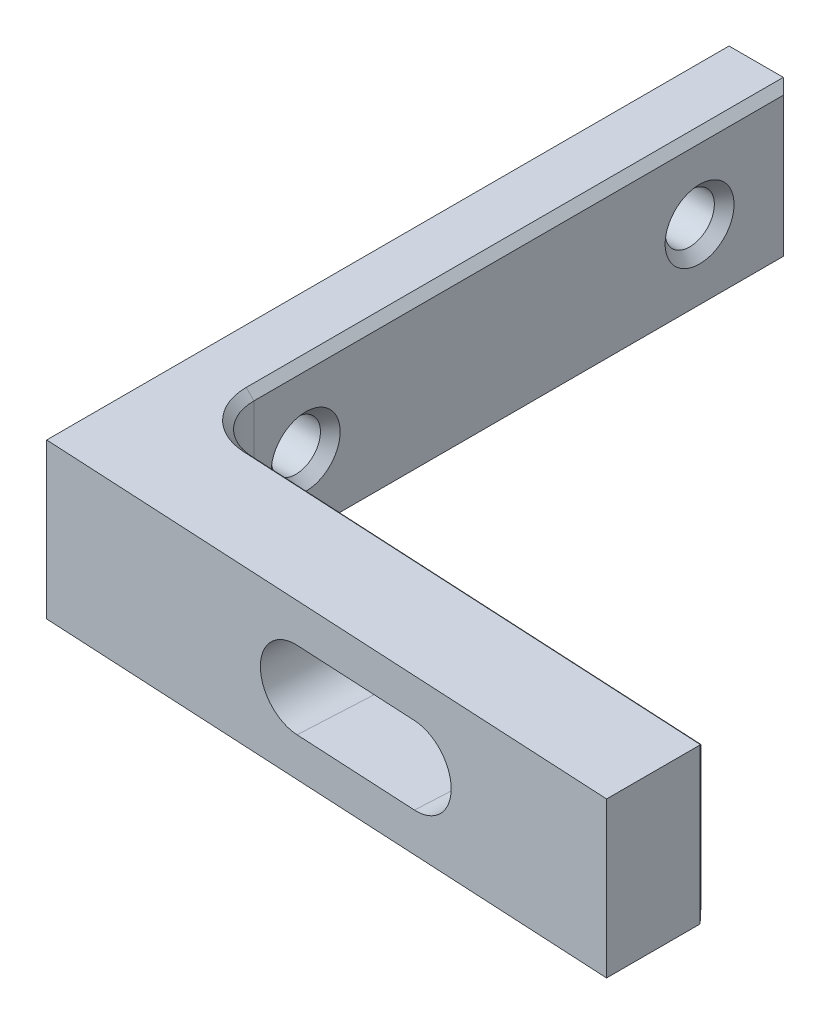
SolidWorks part; units mm, degrees
ref_plane "Front Plane" through (0, 0, 0) normal (0, 0, 1) x (1, 0, 0)
ref_plane "Top Plane" through (0, 0, 0) normal (0, 1, 0) x (1, 0, 0)
ref_plane "Right Plane" through (0, 0, 0) normal (1, 0, 0) x (0, 0, -1)
sketch "Sketch1" plane through (0, 0, 0) normal (0, 1, 0) x (1, 0, 0)
  line L1 (-19.05, -22) -> (19.05, -22)
  line L2 (-19.05, -22) -> (-19.05, 22)
  line L3 (-19.05, 22) -> (19.05, 22)
  line L4 (19.05, -22) -> (19.05, 22)
  line L5 (-19.05, -22) -> (19.05, 22) construction
  line L6 (-19.05, 22) -> (19.05, -22) construction
  point P0 (0, 0)
  dimension "D1" = 38.1
  dimension "D2" = 44
extrude "Boss-Extrude1" add sketch "Sketch1" along normal blind 10
sketch "Sketch2" plane through (0, 10, 0) normal (0, 1, 0) x (1, 0, 0)
  line L0 (-19.05, 22) -> (-19.05, -22) construction
  line L1 (19.05, 22) -> (-15.05, 22)
  line L2 (19.05, 22) -> (19.05, -15.65)
  line L3 (19.05, -15.65) -> (-15.05, -15.65)
  line L4 (-15.05, 22) -> (-15.05, -15.65)
  line L5 (-19.05, -22) -> (19.05, -22) construction
  dimension "D1" = 4
  dimension "D2" = 6.35
extrude "Cut-Extrude1" cut sketch "Sketch2" against normal up to next
hole_wizard "1/8 (0.125) Diameter Hole1" positions "Sketch4" profile "Sketch3" hole size "1/8" standard "Ansi Inch" end condition through all
sketch "Sketch4" plane through (-19.05, 0, 0) normal (-1, 0, 0) x (0, 0, 1)
  line L1 (-22, 5) -> (-16.1, 5) construction
  line L2 (-22, 10) -> (-22, 0) construction
  line L3 (9.3, 5) -> (-16.1, 5) construction
  line L4 (15.65, 0) -> (15.65, 10) construction
  point P0 (-16.1, 5)
  point P1 (9.3, 5)
  dimension "D1" = 6.35
  dimension "D2" = 25.4
sketch "Sketch3" plane through (-19.05, 5, -16.1) normal (0, 1, 0) x (0, 0, 1)
  line L0 (0, 0) -> (0, 4)
  line L1 (0, 4) -> (2.2225, 4)
  line L2 (1.5875, 3.365) -> (1.5875, 0.635)
  line L3 (1.5875, 0.635) -> (2.2225, 0)
  line L5 (2.2225, 0) -> (0, 0)
  line L6 (-1.5875, 0.635) -> (-2.2225, 0) construction
  line L7 (2.2225, 4) -> (1.5875, 3.365)
  line L8 (-2.2225, 4) -> (-1.5875, 3.365) construction
  line L11 (0, -6.35) -> (0, 107.95) construction
  dimension "Thru Hole Dia." = 3.175
  dimension "Thru Hole Depth" = 4
  dimension "Near C'Sink Dia." = 4.445
  dimension "Near C'Sink Angle" = 90
  dimension "Far C'Sink Dia." = 4.445
  dimension "Far C'Sink Angle" = 90
draft "Draft1" type of draft neutral plane draft angle 3 faces to draft 1 face at (0, 5, 22) neutral plane through (-19.05, 10, 22) neutral plane normal (-1, 0, 0) parameters "D1"=3
sketch "Sketch7" plane through (0, 10, 0) normal (0, 1, 0) x (1, 0, 0)
  line L0 (-15.05, -15.65) -> (19.05, -15.65) construction
  line L1 (-15.05, -15.65) -> (19.05, -15.65)
  line L2 (19.05, -23.9967) -> (19.05, -15.65) construction
  line L3 (19.05, -17.4371) -> (19.05, -15.65)
  line L4 (-15.05, -15.65) -> (19.05, -17.4371)
  line L5 (-19.05, -22) -> (19.05, -23.9967) construction
extrude "Cut-Extrude2" cut sketch "Sketch7" against normal through all
sketch "Sketch8" plane through (-0.8592, 0, 16.3937) normal (0.0523, 0, -0.9986) x (-0.9986, 0, -0.0523)
  line L0 (-7.1897, 5) -> (0.8103, 5) construction
  line L1 (-7.1897, 7.5) -> (0.8103, 7.5)
  line L2 (-7.1897, 2.5) -> (0.8103, 2.5)
  line L3 (-19.9365, 5) -> (-7.1897, 5) construction
  line L4 (-19.9365, 0) -> (-19.9365, 10) construction
  line L8 (14.2103, 0) -> (14.2103, 10) construction
  arc A0 (-7.1897, 7.5) -> (-7.1897, 2.5) centre (-7.1897, 5) ccw
  arc A1 (0.8103, 2.5) -> (0.8103, 7.5) centre (0.8103, 5) ccw
  point P2 (-3.1897, 5)
  dimension "D2" = 8
  dimension "D1" = 5
  dimension "D3" = 21.4
extrude "Cut-Extrude3" cut sketch "Sketch8" against normal through all
fillet "Fillet2" radius 3.175 1 edges at (-15.05, 5, 15.65)
chamfer "Chamfer1" distance 0.5 angle 45 4 edges at (2.3262, 7.5, 16.5606) (8.8172, 5, 16.9008) (-4.1649, 5, 16.2205) (2.3262, 2.5, 16.5606)
chamfer "Chamfer2" distance 0.5 angle 45 8 edges at (19.05, 5, 17.4371) (3.5044, 10, 16.6224) (3.5044, 0, 16.6224) (-14.1781, 10, 14.8226) (-14.1781, 0, 14.8226) (-15.05, 10, -4.6815) (-15.05, 5, -22) (-15.05, 0, -4.6815)
